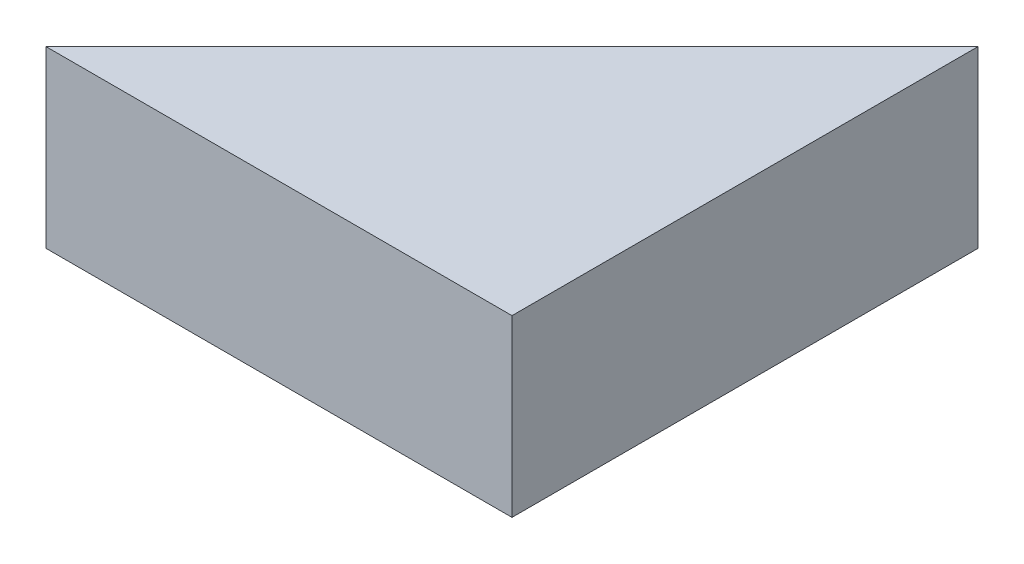
SolidWorks part; units mm, degrees
ref_plane "Front Plane" through (0, 0, 0) normal (0, 0, 1) x (1, 0, 0)
ref_plane "Top Plane" through (0, 0, 0) normal (0, 1, 0) x (1, 0, 0)
ref_plane "Right Plane" through (0, 0, 0) normal (1, 0, 0) x (0, 0, -1)
sketch "Sketch1" plane through (0, 0, 0) normal (0, 1, 0) x (1, 0, 0)
  line L0 (0, 0) -> (0, 80)
  line L1 (0, 80) -> (-80, 0)
  line L2 (-80, 0) -> (0, 0)
  dimension "D1" = 80
extrude "Boss-Extrude1" add sketch "Sketch1" along normal blind 30
